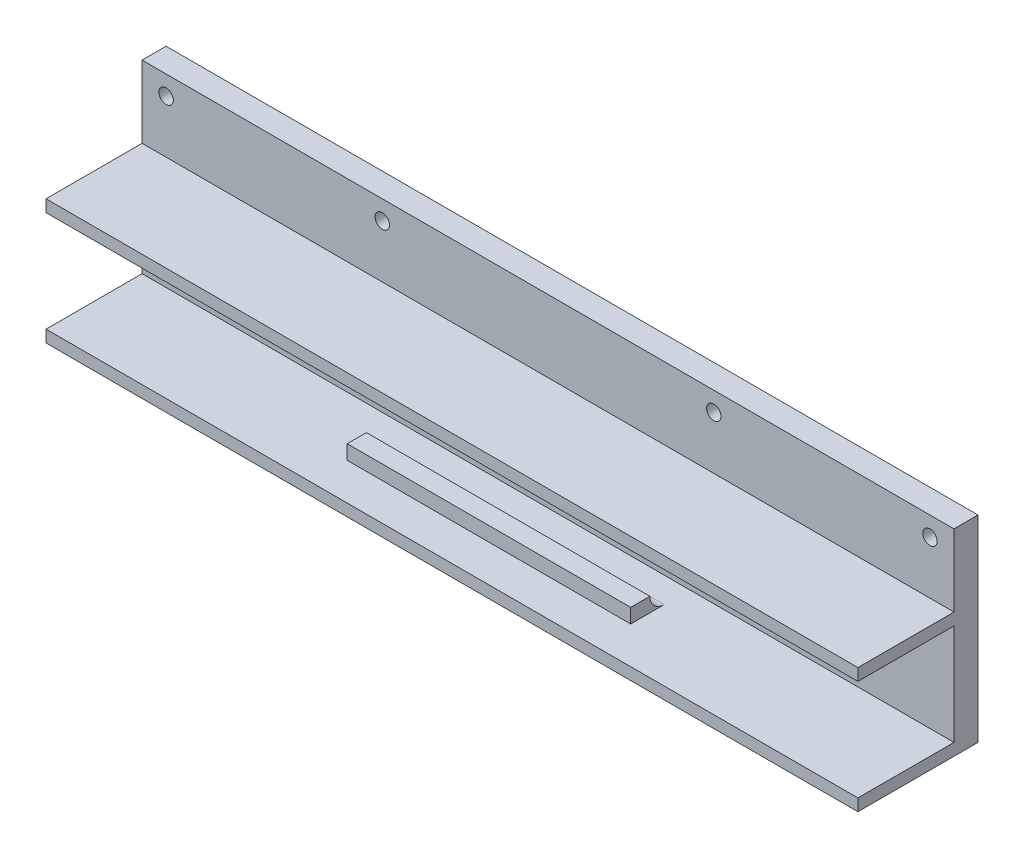
SolidWorks part; units mm, degrees
ref_plane "Спереди" through (0, 0, 0) normal (0, 0, 1) x (1, 0, 0)
ref_plane "Сверху" through (0, 0, 0) normal (0, 1, 0) x (1, 0, 0)
ref_plane "Справа" through (0, 0, 0) normal (1, 0, 0) x (0, 0, -1)
sketch "Эскиз1" plane through (0, 0, 0) normal (0, 0, 1) x (1, 0, 0)
  line L1 (-84.5, -20.5) -> (84.5, -20.5)
  line L2 (-84.5, -20.5) -> (-84.5, 20.5)
  line L3 (-84.5, 20.5) -> (84.5, 20.5)
  line L4 (84.5, -20.5) -> (84.5, 20.5)
  line L5 (0, 20.5) -> (0, -20.5) construction
  line L6 (-84.5, 0) -> (84.5, 0) construction
  point P0 (0, 0)
  dimension "D1" = 41
  dimension "D2" = 169
extrude "Бобышка-Вытянуть2" add sketch "Эскиз1" along normal blind 5
sketch "Эскиз3" plane through (0, 0, 5) normal (0, 0, 1) x (1, 0, 0)
  line L0 (84.5, -20.5) -> (84.5, 20.5) construction
  line L1 (84.5, 20.5) -> (-84.5, 20.5) construction
  line L2 (-84.5, 20.5) -> (-84.5, -20.5) construction
  circle A0 centre (79.5, 16.5) radius 1.5
  circle A1 centre (34.5, 16.5) radius 1.5
  circle A2 centre (-34.5, 16.5) radius 1.5
  circle A3 centre (-79.5, 16.5) radius 1.5
  point P14 (0, 0)
  dimension "D1" = 3
  dimension "D4" = 3
  dimension "D7" = 3
  dimension "D11" = 3
  dimension "D2" = 5
  dimension "D3" = 4
  dimension "D5" = 4
  dimension "D6" = 45
  dimension "D8" = 5
  dimension "D9" = 4
  dimension "D10" = 45
  dimension "D12" = 4
extrude "Вырез-Вытянуть1" cut sketch "Эскиз3" against normal blind 5
sketch "Эскиз4" plane through (0, 0, 5) normal (0, 0, 1) x (1, 0, 0)
  line L0 (84.5, -20.5) -> (84.5, 20.5) construction
  line L1 (-84.5, -20.5) -> (84.5, -20.5)
  line L2 (-84.5, -20.5) -> (-84.5, 5.5)
  line L3 (-84.5, 5.5) -> (84.5, 5.5)
  line L4 (84.5, -20.5) -> (84.5, 5.5)
  line L5 (0, 5.5) -> (0, -20.5) construction
  line L6 (-84.5, -7.5) -> (84.5, -7.5) construction
  point P476 (0, -7.5)
  dimension "D1" = 26
extrude "Бобышка-Вытянуть3" add sketch "Эскиз4" along normal blind 20
sketch "Эскиз5" plane through (-84.5, 0, 0) normal (-1, 0, 0) x (0, 0, 1)
  line L0 (25, 5.5) -> (25, -20.5) construction
  line L1 (25, -18) -> (5, -18)
  line L2 (25, -18) -> (25, 3)
  line L3 (25, 3) -> (5, 3)
  line L4 (5, -18) -> (5, 3)
  line L5 (15, 3) -> (15, -18) construction
  line L6 (25, -7.5) -> (5, -7.5) construction
  line L7 (25, -20.5) -> (0, -20.5) construction
  line L8 (25, 5.5) -> (5, 5.5) construction
  line L9 (0, 20.5) -> (0, -20.5) construction
  point P284 (15, -7.5)
  dimension "D1" = 2.5
  dimension "D2" = 2.5
  dimension "D3" = 5
extrude "Вырез-Вытянуть2" cut sketch "Эскиз5" against normal blind 55
sketch "Эскиз6" plane through (84.5, 0, 0) normal (1, 0, 0) x (0, 0, -1)
  line L0 (-25, -20.5) -> (-25, 5.5) construction
  line L1 (-25, 3) -> (-5, 3)
  line L2 (-25, 3) -> (-25, -18)
  line L3 (-25, -18) -> (-5, -18)
  line L4 (-5, 3) -> (-5, -18)
  line L5 (-15, -18) -> (-15, 3) construction
  line L6 (-25, -7.5) -> (-5, -7.5) construction
  line L7 (0, -20.5) -> (0, 20.5) construction
  line L8 (-25, 5.5) -> (-5, 5.5) construction
  line L9 (-25, -20.5) -> (0, -20.5) construction
  point P192 (-15, -7.5)
  dimension "D1" = 5
  dimension "D2" = 2.5
  dimension "D3" = 2.5
extrude "Вырез-Вытянуть3" cut sketch "Эскиз6" against normal blind 55
sketch "Эскиз7" plane through (29.5, 0, 0) normal (1, 0, 0) x (0, 0, -1)
  line L1 (-5, 3) -> (-10.3, 3)
  line L2 (-5, 3) -> (-5, -18)
  line L3 (-5, -18) -> (-10.3, -18)
  line L4 (-13.3, 0) -> (-13.3, -15)
  line L5 (-9.15, -18) -> (-9.15, 3) construction
  line L6 (-5, -7.5) -> (-13.3, -7.5) construction
  arc A0 (-10.3, 3) -> (-13.3, 0) centre (-10.3, 0) ccw
  arc A1 (-10.3, -18) -> (-13.3, -15) centre (-10.3, -15) cw
  point P296 (-9.15, -7.5)
  dimension "D2" = 6
  dimension "D1" = 8.3
  dimension "D3" = 3
  dimension "D4" = 3
extrude "Вырез-Вытянуть6" cut sketch "Эскиз7" against normal blind 59
sketch "Эскиз10" plane through (29.5, 0, 0) normal (1, 0, 0) x (0, 0, -1)
  line L0 (-25, -18) -> (-10.3, -18) construction
  line L1 (-25, 3) -> (-17.3, 3)
  line L2 (-25, 3) -> (-25, -18)
  line L3 (-25, -18) -> (-17.3, -18)
  line L4 (-17.3, 3) -> (-17.3, -18)
  line L5 (-21.15, -18) -> (-21.15, 3) construction
  line L6 (-25, -7.5) -> (-17.3, -7.5) construction
  line L7 (-13.3, 0) -> (-13.3, -15) construction
  point P500 (-21.15, -7.5)
  dimension "D1" = 0
  dimension "D2" = 4
extrude "Вырез-Вытянуть7" cut sketch "Эскиз10" against normal blind 59
sketch "Эскиз11" plane through (29.5, 0, 0) normal (1, 0, 0) x (0, 0, -1)
  line L0 (-17.3, -18) -> (-17.3, 3) construction
  line L1 (-17.3, 0) -> (-13.3, 0)
  line L2 (-17.3, 0) -> (-17.3, -15)
  line L3 (-17.3, -15) -> (-13.3, -15)
  line L4 (-13.3, 0) -> (-13.3, -15)
  line L5 (-15.3, -15) -> (-15.3, 0) construction
  line L6 (-17.3, -7.5) -> (-13.3, -7.5) construction
  line L7 (-13.3, 0) -> (-13.3, -15) construction
  line L8 (-25, -18) -> (-5, -18) construction
  line L9 (-10.3, 3) -> (-17.3, 3) construction
  point P476 (-15.3, -7.5)
  dimension "D1" = 3
  dimension "D2" = 3
extrude "Вырез-Вытянуть8" cut sketch "Эскиз11" against normal blind 59
